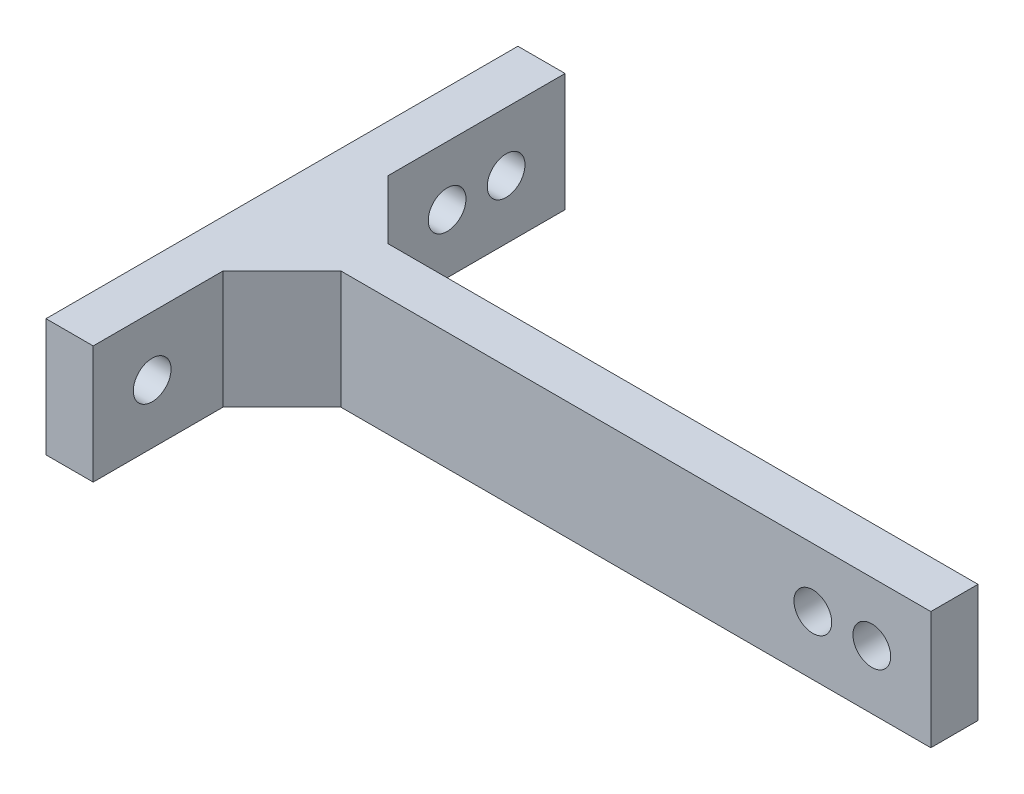
SolidWorks part; units mm, degrees
ref_plane "正面" through (0, 0, 0) normal (0, 0, 1) x (1, 0, 0)
ref_plane "平面" through (0, 0, 0) normal (0, 1, 0) x (1, 0, 0)
ref_plane "右側面" through (0, 0, 0) normal (1, 0, 0) x (0, 0, -1)
sketch "ｽｹｯﾁ1" plane through (0, 0, 0) normal (0, 0, 1) x (1, 0, 0)
  line L1 (-23.0203, 2.4594) -> (31.9797, 2.4594)
  line L2 (-23.0203, 2.4594) -> (-23.0203, -7.5406)
  line L3 (-23.0203, -7.5406) -> (31.9797, -7.5406)
  line L4 (31.9797, 2.4594) -> (31.9797, -7.5406)
  dimension "D1" = 55
  dimension "D2" = 10
extrude "ﾎﾞｽ - 押し出し1" add sketch "ｽｹｯﾁ1" along normal blind 4
sketch "ｽｹｯﾁ2" plane through (-23.0203, 0, 0) normal (-1, 0, 0) x (0, 0, 1)
  line L0 (4, 2.4594) -> (0, 2.4594) construction
  line L1 (-20, 2.4594) -> (20, 2.4594)
  line L2 (-20, 2.4594) -> (-20, -7.5406)
  line L3 (-20, -7.5406) -> (20, -7.5406)
  line L4 (20, 2.4594) -> (20, -7.5406)
  line L5 (4, -7.5406) -> (0, -7.5406) construction
  line L6 (0, 2.4594) -> (0, -7.5406) construction
  dimension "D1" = 0
  dimension "D2" = 0
  dimension "D3" = 20
  dimension "D4" = 40
extrude "ﾎﾞｽ - 押し出し2" add sketch "ｽｹｯﾁ2" along normal blind 4 contours L1 L4 L3 L2
sketch "ｽｹｯﾁ3" plane through (0, 2.4594, 0) normal (0, 1, 0) x (1, 0, 0)
  line L0 (-23.0203, 5) -> (-18.0203, 0)
  line L1 (31.9797, 0) -> (-23.0203, 0) construction
  line L10 (31.9797, 0) -> (-23.0203, 0)
  line L11 (-23.0203, 0) -> (-23.0203, 20)
  line L12 (-23.0203, 20) -> (-27.0203, 20)
  line L13 (-27.0203, 20) -> (-27.0203, -20)
  line L14 (-27.0203, -20) -> (-23.0203, -20)
  line L15 (-23.0203, -20) -> (-23.0203, -4)
  line L16 (-23.0203, -4) -> (31.9797, -4)
  line L17 (31.9797, -4) -> (31.9797, 0)
  line L18 (-18.0203, 0) -> (-23.0203, 0)
  line L19 (-23.0203, 0) -> (-23.0203, 5)
  dimension "D1" = 5
  dimension "D3" = 5
  dimension "D2" = 0
extrude "ﾎﾞｽ - 押し出し3" add sketch "ｽｹｯﾁ3" against normal blind 10 contours L0 L18 L19
ref_plane "平面3" through (-23.0203, -7.5406, 4) normal (1, 0, 0) x (0, 0, -1)
sketch "ｽｹｯﾁ6" plane through (0, -7.5406, 0) normal (0, -1, 0) x (1, 0, 0)
  line L0 (-23.0203, 9) -> (-18.0203, 4)
  line L1 (-23.0203, 4) -> (-23.0203, 20) construction
  line L2 (-23.0203, 4) -> (31.9797, 4) construction
  line L12 (-23.0203, -5) -> (-18.0203, 0)
  line L13 (-18.0203, 0) -> (31.9797, 0)
  line L14 (31.9797, 0) -> (31.9797, 4)
  line L15 (31.9797, 4) -> (-23.0203, 4)
  line L16 (-23.0203, 4) -> (-23.0203, 20)
  line L17 (-23.0203, 20) -> (-27.0203, 20)
  line L18 (-27.0203, 20) -> (-27.0203, -20)
  line L19 (-27.0203, -20) -> (-23.0203, -20)
  line L20 (-23.0203, -20) -> (-23.0203, -5)
  line L21 (-23.0203, -5) -> (-18.0203, 0)
  line L22 (-18.0203, 0) -> (31.9797, 0)
  line L23 (31.9797, 0) -> (31.9797, 4)
  line L24 (31.9797, 4) -> (-18.0203, 4)
  line L25 (-23.0203, 9) -> (-23.0203, 20)
  line L26 (-23.0203, 20) -> (-27.0203, 20)
  line L27 (-27.0203, 20) -> (-27.0203, -20)
  line L28 (-27.0203, -20) -> (-23.0203, -20)
  line L29 (-23.0203, -20) -> (-23.0203, -5)
  dimension "D1" = 5
  dimension "D2" = 5
  dimension "D3" = 0
extrude "ﾎﾞｽ - 押し出し5" add sketch "ｽｹｯﾁ6" against normal blind 10 contours L0 L24 L23 L22 L21 L29 L28 L27 L26 L25
sketch "ｽｹｯﾁ4" plane through (0, 0, 4) normal (0, 0, 1) x (1, 0, 0)
  line L0 (31.9797, 2.4594) -> (-18.0203, 2.4594) construction
  line L1 (31.9797, -7.5406) -> (31.9797, 2.4594) construction
  circle A0 centre (26.9797, -2.5406) radius 1.6
  circle A1 centre (21.9797, -2.5406) radius 1.6
  dimension "D1" = 5
  dimension "D2" = 5
  dimension "D3" = 2
extrude "ｶｯﾄ - 押し出し1" cut sketch "ｽｹｯﾁ4" against normal blind 5
sketch "ｽｹｯﾁ7" plane through (-23.0203, 0, 0) normal (1, 0, 0) x (0, 0, -1)
  line L0 (-20, 2.4594) -> (-20, -7.5406) construction
  line L1 (-9, 2.4594) -> (-20, 2.4594) construction
  circle A0 centre (-15, -2.5406) radius 1.6
  circle A1 centre (10, -2.5406) radius 1.6
  circle A2 centre (15, -2.5406) radius 1.6
  dimension "D1" = 5
  dimension "D2" = 5
  dimension "D3" = 2
  dimension "D4" = 2
extrude "ｶｯﾄ - 押し出し2" cut sketch "ｽｹｯﾁ7" against normal blind 4
